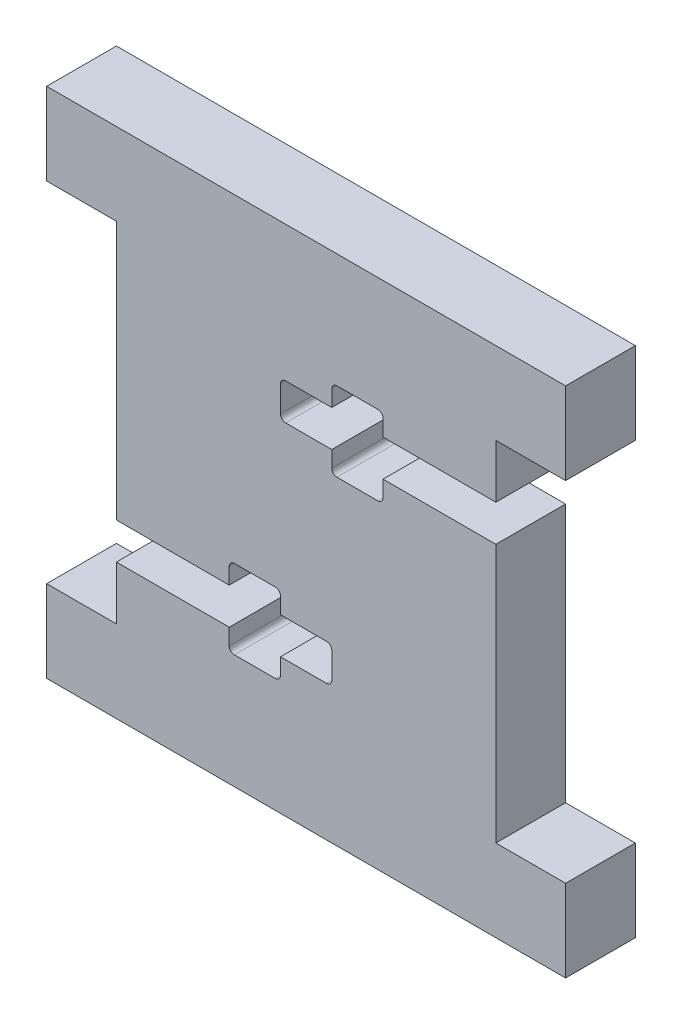
SolidWorks part; units mm, degrees
ref_plane "Front Plane" through (0, 0, 0) normal (0, 0, 1) x (1, 0, 0)
ref_plane "Top Plane" through (0, 0, 0) normal (0, 1, 0) x (1, 0, 0)
ref_plane "Right Plane" through (0, 0, 0) normal (1, 0, 0) x (0, 0, -1)
sketch "Sketch1" plane through (0, 0, 0) normal (0, 0, 1) x (1, 0, 0)
  line L1 (25.3, -25) -> (-25.3, -25)
  line L2 (25.3, -25) -> (25.3, 25)
  line L3 (25.3, 25) -> (-25.3, 25)
  line L4 (-25.3, -25) -> (-25.3, 25)
  line L5 (25.3, -25) -> (-25.3, 25) construction
  line L6 (25.3, 25) -> (-25.3, -25) construction
  point P0 (0, 0)
  dimension "D1" = 50.6
  dimension "D2" = 50
extrude "Boss-Extrude1" add sketch "Sketch1" along normal blind 6.8
sketch "Sketch2" plane through (0, 0, 6.8) normal (0, 0, 1) x (1, 0, 0)
  line L0 (25.3, -25) -> (25.3, 25) construction
  line L1 (18.5, -17) -> (25.3, -17)
  line L2 (18.5, -17) -> (18.5, 17)
  line L3 (18.5, 17) -> (25.3, 17)
  line L4 (25.3, -17) -> (25.3, 17)
  line L5 (18.5, -17) -> (25.3, 17) construction
  line L6 (18.5, 17) -> (25.3, -17) construction
  point P0 (21.9, 0)
  dimension "D1" = 34
  dimension "D2" = 6.8
extrude "Cut-Extrude1" cut sketch "Sketch2" against normal blind 6.8
mirror "Mirror1" about plane through (0, 0, 0) normal (1, 0, 0) of "Cut-Extrude1"
sketch "Sketch3" plane through (0, 0, 6.8) normal (0, 0, 1) x (1, 0, 0)
  line L0 (18.5, 17) -> (18.5, -17) construction
  line L1 (-2.5, 8.225) -> (18.5, 8.225)
  line L2 (-2.5, 8.225) -> (-2.5, 11.775)
  line L3 (-2.5, 11.775) -> (18.5, 11.775)
  line L4 (18.5, 8.225) -> (18.5, 11.775)
  line L5 (-2.5, 8.225) -> (18.5, 11.775) construction
  line L6 (-2.5, 11.775) -> (18.5, 8.225) construction
  line L7 (-18.5, 17) -> (-18.5, -17) construction
  line L8 (2.5, -11.775) -> (-18.5, -11.775)
  line L9 (2.5, -11.775) -> (2.5, -8.225)
  line L10 (2.5, -8.225) -> (-18.5, -8.225)
  line L11 (-18.5, -11.775) -> (-18.5, -8.225)
  line L12 (2.5, -11.775) -> (-18.5, -8.225) construction
  line L13 (2.5, -8.225) -> (-18.5, -11.775) construction
  line L14 (25.3, 25) -> (-25.3, 25) construction
  line L15 (-25.3, -25) -> (25.3, -25) construction
  line L17 (-2.5, -13.86) -> (-7.5, -13.86)
  line L18 (-2.5, -13.86) -> (-2.5, -6.14)
  line L19 (-2.5, -6.14) -> (-7.5, -6.14)
  line L20 (-7.5, -13.86) -> (-7.5, -6.14)
  line L21 (-2.5, -13.86) -> (-7.5, -6.14) construction
  line L22 (-2.5, -6.14) -> (-7.5, -13.86) construction
  line L23 (2.5, 6.14) -> (7.5, 6.14)
  line L24 (2.5, 6.14) -> (2.5, 13.86)
  line L25 (2.5, 13.86) -> (7.5, 13.86)
  line L26 (7.5, 6.14) -> (7.5, 13.86)
  line L27 (2.5, 6.14) -> (7.5, 13.86) construction
  line L28 (2.5, 13.86) -> (7.5, 6.14) construction
  point P0 (8, 10)
  point P7 (-8, -10)
  point P18 (-5, -10)
  point P23 (5, 10)
  line M13 (-18.5, 17) -> (-18.5, -17)
  line M19 (18.5, -17) -> (18.5, 17)
  dimension "D1" = 3.55
  dimension "D2" = 21
  dimension "D3" = 15
  dimension "D4" = 15
  dimension "D5" = 11
  dimension "D6" = 11
  dimension "D7" = 5
  dimension "D8" = 7.72
extrude "Cut-Extrude2" cut sketch "Sketch3" against normal blind 6.8 contours L18 L8 L9 L10 | L20 L17 L18 L8 | L8 L20 L10 M13 | L20 L10 L18 L19 | L20 L8 L18 L10 | L1 L26 L3 L24 | L1 L24 L3 L2 | L23 L26 L1 L24 | L3 L26 L25 L24 | L26 L1 L3 M19
fillet "Fillet1" radius 0.5 12 edges at (-2.5, -6.14, 3.4) (-7.5, -6.14, 3.4) (-7.5, -13.86, 3.4) (-2.5, -13.86, 3.4) (2.5, -11.775, 3.4) (2.5, -8.225, 3.4) (-2.5, 8.225, 3.4) (-2.5, 11.775, 3.4) (2.5, 13.86, 3.4) (7.5, 13.86, 3.4) (7.5, 6.14, 3.4) (2.5, 6.14, 3.4)
